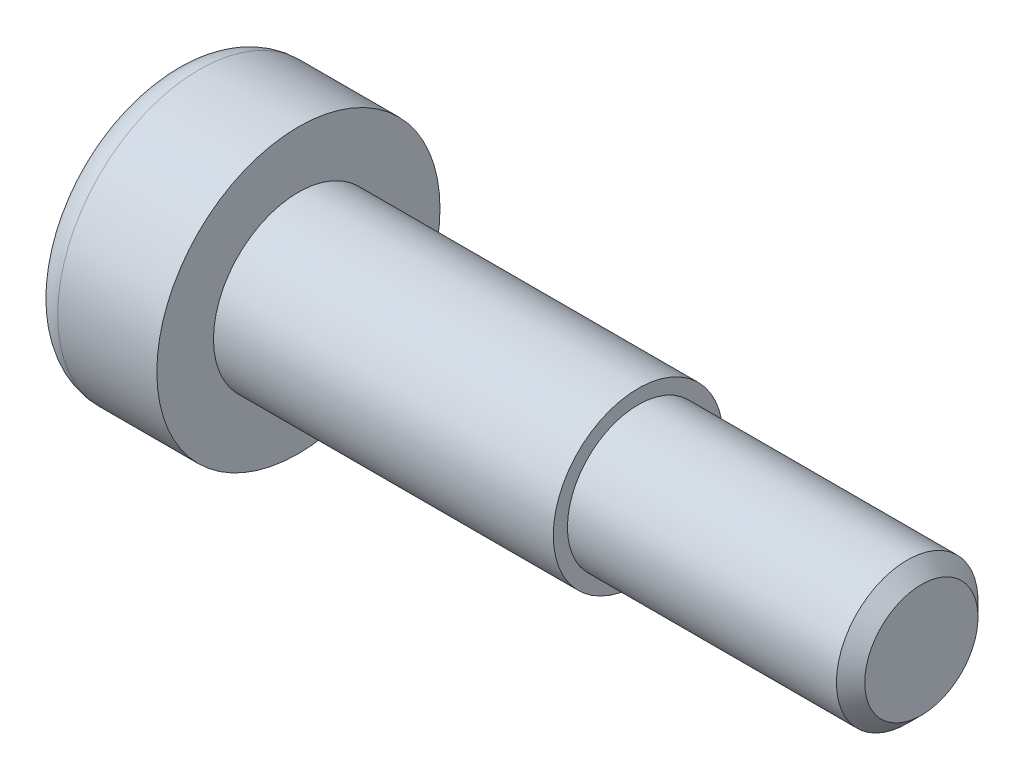
SolidWorks part; units mm, degrees
material "不锈钢 (铁素体)"
ref_plane "前视基准面" through (0, 0, 0) normal (0, 0, 1) x (1, 0, 0)
ref_plane "上视基准面" through (0, 0, 0) normal (0, 1, 0) x (1, 0, 0)
ref_plane "右视基准面" through (0, 0, 0) normal (1, 0, 0) x (0, 0, -1)
sketch "草图1" plane through (0, 0, 0) normal (0, 0, 1) x (1, 0, 0)
  line L0 (0, 0) -> (26.5, 0) construction
  line L1 (0, 0) -> (0, 5)
  line L2 (0, 5) -> (4.5, 5)
  line L3 (4.5, 5) -> (4.5, 3)
  line L4 (4.5, 3) -> (16.5, 3)
  line L5 (16.5, 3) -> (16.5, 2.5)
  line L6 (16.5, 2.5) -> (26.5, 2.5)
  line L7 (26.5, 2.5) -> (26.5, 0)
  line L8 (0, 0) -> (26.5, 0)
  dimension "D1" = 10
  dimension "D2" = 6
  dimension "D3" = 5
  dimension "D4" = 10
  dimension "D5" = 4.5
  dimension "D6" = 12
revolve "旋转1" add sketch "草图1" angle 360 about L0
cosmetic thread "装饰螺纹线1" parameters "D2"=4.134
sketch "草图2" plane through (0, 0, 0) normal (-1, 0, 0) x (0, 0, 1)
  line L0 (0, 0) -> (0, 1.7321) construction
  line L1 (0, 1.7321) -> (-1.5, 0.866)
  line L2 (-1.5, 0.866) -> (-1.5, -0.866)
  line L3 (-1.5, -0.866) -> (0, -1.7321)
  line L4 (0, -1.7321) -> (1.5, -0.866)
  line L5 (1.5, -0.866) -> (1.5, 0.866)
  line L6 (1.5, 0.866) -> (0, 1.7321)
  circle A0 centre (0, 0) radius 1.5 construction
  dimension "D1" = 3
extrude "切除-拉伸1" cut sketch "草图2" against normal blind 3
fillet "圆角1" radius 1 1 edges at (0, 0, 5)
chamfer "倒角1" distance 0.5 angle 45 1 edges at (26.5, 0, 2.5)
